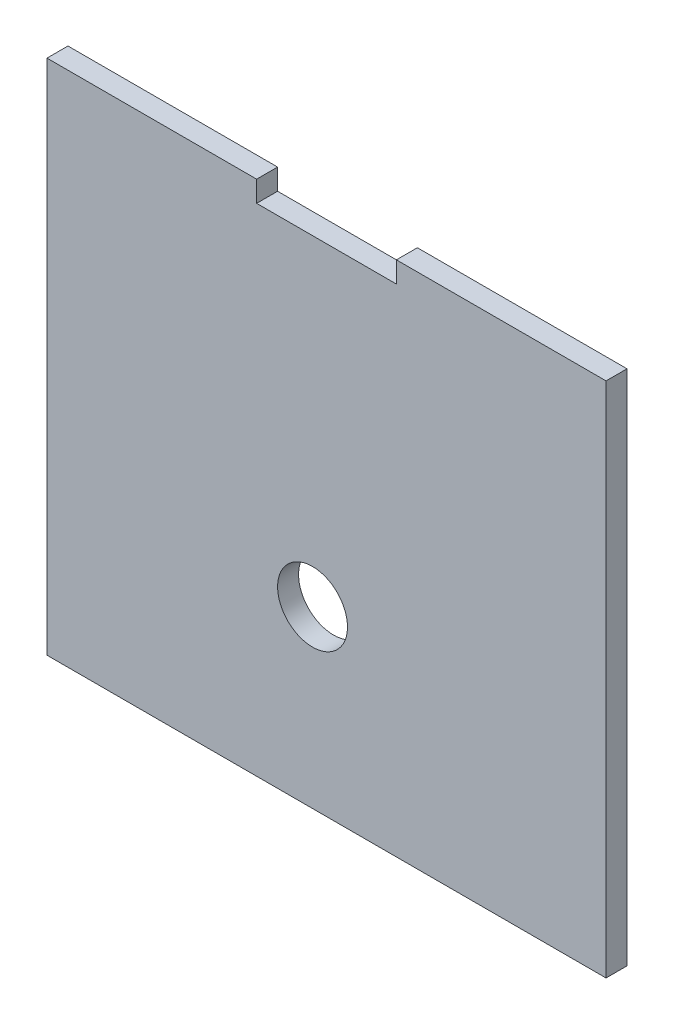
SolidWorks part; units mm, degrees
ref_plane "Plano frontal" through (0, 0, 0) normal (0, 0, 1) x (1, 0, 0)
ref_plane "Plano superior" through (0, 0, 0) normal (0, 1, 0) x (1, 0, 0)
ref_plane "Plano direito" through (0, 0, 0) normal (1, 0, 0) x (0, 0, -1)
sketch "Esboço2" plane through (0, 0, 0) normal (0, 0, 1) x (1, 0, 0)
  line L1 (3, 51.1529) -> (-77, 51.1529)
  line L2 (3, 51.1529) -> (3, -22.8471)
  line L3 (3, -22.8471) -> (-77, -22.8471)
  line L4 (-77, 51.1529) -> (-77, -22.8471)
  line L5 (-47, 51.1529) -> (-27, 51.1529)
  line L6 (-47, 51.1529) -> (-47, 48.1529)
  line L7 (-47, 48.1529) -> (-27, 48.1529)
  line L8 (-27, 51.1529) -> (-27, 48.1529)
  circle A0 centre (-39, 2.1529) radius 5
  dimension "D2" = 25
  dimension "D3" = 10
  dimension "D4" = 38
  dimension "D5" = 42
  dimension "D1" = 80
  dimension "D6" = 74
  dimension "D7" = 0
  dimension "D8" = 20
  dimension "D9" = 3
  dimension "D10" = 30
  dimension "D11" = 30
extrude "Ressalto-extrusão1" add sketch "Esboço2" along normal blind 3 contours L1 L8 L7 L6 L4 L3 L2 A0
